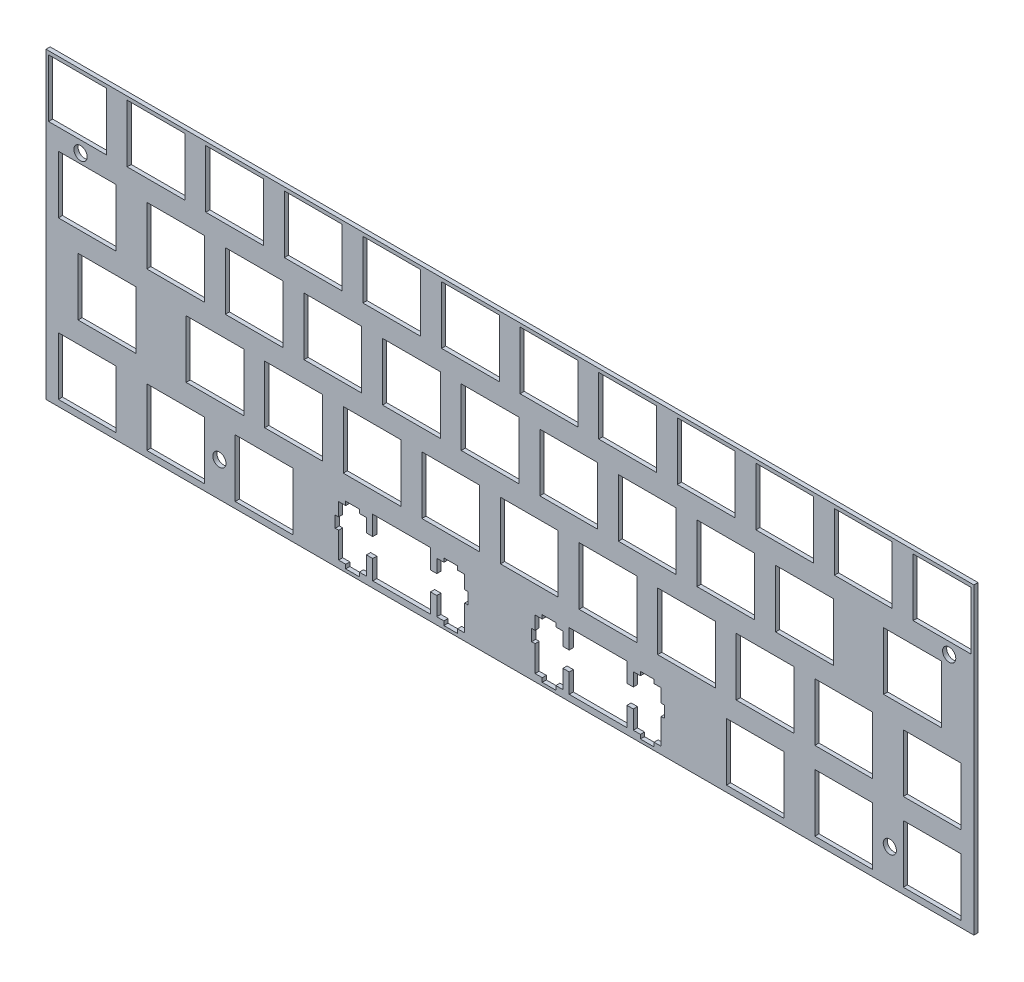
SolidWorks part; units mm, degrees
ref_plane "前视基准面" through (0, 0, 0) normal (0, 0, 1) x (1, 0, 0)
ref_plane "上视基准面" through (0, 0, 0) normal (0, 1, 0) x (1, 0, 0)
ref_plane "右视基准面" through (0, 0, 0) normal (1, 0, 0) x (0, 0, -1)
sketch "Model" plane through (0, 0, 0) normal (0, 0, 1) x (1, 0, 0)
  line L0 (227.4046, 0.7758) -> (227.4046, 75.2929) construction
  line L1 (2.0031, 74.7929) -> (226.9046, 74.7929)
  line L2 (2.0031, 74.7929) -> (2.0031, 1.2758)
  line L3 (2.0031, 1.2758) -> (226.9046, 1.2758)
  line L4 (81.201, 16.7831) -> (81.201, 12.0826)
  line L5 (81.201, 12.0826) -> (79.6756, 12.0826)
  line L6 (79.6756, 12.0826) -> (79.6756, 15.3128)
  line L7 (79.6756, 15.3128) -> (77.9501, 15.3128)
  line L8 (77.9501, 15.3128) -> (77.9501, 16.2347)
  line L9 (77.9501, 16.2347) -> (74.651, 16.2347)
  line L10 (74.651, 16.2347) -> (74.651, 15.3128)
  line L11 (74.651, 15.3128) -> (72.9259, 15.3128)
  line L12 (72.9259, 15.3128) -> (72.9259, 12.0826)
  line L13 (72.9259, 12.0826) -> (72.1004, 12.0826)
  line L14 (72.1004, 12.0826) -> (72.1004, 9.2838)
  line L15 (72.1004, 9.2838) -> (72.9259, 9.2838)
  line L16 (72.9259, 9.2838) -> (72.9259, 3.0138)
  line L17 (72.9259, 3.0138) -> (74.651, 3.0138)
  line L18 (74.651, 3.0138) -> (74.651, 2.0326)
  line L19 (74.651, 2.0326) -> (77.9501, 2.0326)
  line L20 (77.9501, 2.0326) -> (77.9501, 3.0138)
  line L21 (77.9501, 3.0138) -> (79.6756, 3.0138)
  line L22 (79.6756, 3.0138) -> (79.6756, 7.4827)
  line L23 (79.6756, 7.4827) -> (81.201, 7.4827)
  line L24 (81.201, 7.4827) -> (81.201, 2.7836)
  line L25 (81.201, 2.7836) -> (95.2003, 2.7836)
  line L26 (95.2003, 2.7836) -> (95.2003, 7.4827)
  line L27 (95.2003, 7.4827) -> (96.726, 7.4827)
  line L28 (96.726, 7.4827) -> (96.726, 3.0138)
  line L29 (96.726, 3.0138) -> (98.4497, 3.0138)
  line L30 (98.4497, 3.0138) -> (98.4497, 2.0326)
  line L31 (98.4497, 2.0326) -> (101.75, 2.0326)
  line L32 (101.75, 2.0326) -> (101.75, 3.0138)
  line L33 (101.75, 3.0138) -> (103.475, 3.0138)
  line L34 (103.475, 3.0138) -> (103.475, 9.2838)
  line L35 (103.475, 9.2838) -> (104.301, 9.2838)
  line L36 (104.301, 9.2838) -> (104.301, 12.0826)
  line L37 (104.301, 12.0826) -> (103.475, 12.0826)
  line L38 (103.475, 12.0826) -> (103.475, 15.3128)
  line L39 (103.475, 15.3128) -> (101.75, 15.3128)
  line L40 (101.75, 15.3128) -> (101.75, 16.2347)
  line L41 (101.75, 16.2347) -> (98.4497, 16.2347)
  line L42 (98.4497, 16.2347) -> (98.4497, 15.3128)
  line L43 (98.4497, 15.3128) -> (96.726, 15.3128)
  line L44 (96.726, 15.3128) -> (96.726, 12.0826)
  line L45 (96.726, 12.0826) -> (95.2003, 12.0826)
  line L46 (95.2003, 12.0826) -> (95.2003, 16.7831)
  line L47 (95.2003, 16.7831) -> (81.201, 16.7831)
  line L48 (128.826, 16.7831) -> (128.826, 12.0826)
  line L49 (128.826, 12.0826) -> (127.301, 12.0826)
  line L50 (127.301, 12.0826) -> (127.301, 15.3128)
  line L51 (127.301, 15.3128) -> (125.575, 15.3128)
  line L52 (125.575, 15.3128) -> (125.575, 16.2347)
  line L53 (125.575, 16.2347) -> (122.276, 16.2347)
  line L54 (122.276, 16.2347) -> (122.276, 15.3128)
  line L55 (122.276, 15.3128) -> (120.551, 15.3128)
  line L56 (120.551, 15.3128) -> (120.551, 12.0826)
  line L57 (120.551, 12.0826) -> (119.725, 12.0826)
  line L58 (119.725, 12.0826) -> (119.725, 9.2838)
  line L59 (119.725, 9.2838) -> (120.551, 9.2838)
  line L60 (120.551, 9.2838) -> (120.551, 3.0138)
  line L61 (120.551, 3.0138) -> (122.276, 3.0138)
  line L62 (122.276, 3.0138) -> (122.276, 2.0326)
  line L63 (122.276, 2.0326) -> (125.575, 2.0326)
  line L64 (125.575, 2.0326) -> (125.575, 3.0138)
  line L65 (125.575, 3.0138) -> (127.301, 3.0138)
  line L66 (127.301, 3.0138) -> (127.301, 7.4827)
  line L67 (127.301, 7.4827) -> (128.826, 7.4827)
  line L68 (128.826, 7.4827) -> (128.826, 2.7836)
  line L69 (128.826, 2.7836) -> (142.825, 2.7836)
  line L70 (142.825, 2.7836) -> (142.825, 7.4827)
  line L71 (142.825, 7.4827) -> (144.351, 7.4827)
  line L72 (144.351, 7.4827) -> (144.351, 3.0138)
  line L73 (144.351, 3.0138) -> (146.076, 3.0138)
  line L74 (146.076, 3.0138) -> (146.076, 2.0326)
  line L75 (146.076, 2.0326) -> (149.375, 2.0326)
  line L76 (149.375, 2.0326) -> (149.375, 3.0138)
  line L77 (149.375, 3.0138) -> (151.1, 3.0138)
  line L78 (151.1, 3.0138) -> (151.1, 9.2838)
  line L79 (151.1, 9.2838) -> (151.926, 9.2838)
  line L80 (151.926, 9.2838) -> (151.926, 12.0826)
  line L81 (151.926, 12.0826) -> (151.1, 12.0826)
  line L82 (151.1, 12.0826) -> (151.1, 15.3128)
  line L83 (151.1, 15.3128) -> (149.375, 15.3128)
  line L84 (149.375, 15.3128) -> (149.375, 16.2347)
  line L85 (149.375, 16.2347) -> (146.076, 16.2347)
  line L86 (146.076, 16.2347) -> (146.076, 15.3128)
  line L87 (146.076, 15.3128) -> (144.351, 15.3128)
  line L88 (144.351, 15.3128) -> (144.351, 12.0826)
  line L89 (144.351, 12.0826) -> (142.825, 12.0826)
  line L90 (142.825, 12.0826) -> (142.825, 16.7831)
  line L91 (142.825, 16.7831) -> (128.826, 16.7831)
  line L92 (5.0009, 16.7831) -> (19.0004, 16.7831)
  line L93 (19.0004, 16.7831) -> (19.0004, 2.7836)
  line L94 (19.0004, 2.7836) -> (5.0009, 2.7836)
  line L95 (5.0009, 2.7836) -> (5.0009, 16.7831)
  line L96 (26.4322, 16.7831) -> (40.4315, 16.7831)
  line L97 (40.4315, 16.7831) -> (40.4315, 2.7836)
  line L98 (40.4315, 2.7836) -> (26.4322, 2.7836)
  line L99 (26.4322, 2.7836) -> (26.4322, 16.7831)
  line L100 (47.8621, 16.7831) -> (61.8628, 16.7831)
  line L101 (61.8628, 16.7831) -> (61.8628, 2.7836)
  line L102 (61.8628, 2.7836) -> (47.8621, 2.7836)
  line L103 (47.8621, 2.7836) -> (47.8621, 16.7831)
  line L104 (166.926, 16.7831) -> (180.925, 16.7831)
  line L105 (180.925, 16.7831) -> (180.925, 2.7836)
  line L106 (180.925, 2.7836) -> (166.926, 2.7836)
  line L107 (166.926, 2.7836) -> (166.926, 16.7831)
  line L108 (188.357, 16.7831) -> (202.357, 16.7831)
  line L109 (202.357, 16.7831) -> (202.357, 2.7836)
  line L110 (202.357, 2.7836) -> (188.357, 2.7836)
  line L111 (188.357, 2.7836) -> (188.357, 16.7831)
  line L112 (209.787, 16.7831) -> (223.788, 16.7831)
  line L113 (223.788, 16.7831) -> (223.788, 2.7836)
  line L114 (223.788, 2.7836) -> (209.787, 2.7836)
  line L115 (209.787, 2.7836) -> (209.787, 16.7831)
  line L116 (9.762, 35.833) -> (23.7629, 35.833)
  line L117 (23.7629, 35.833) -> (23.7629, 21.8336)
  line L118 (23.7629, 21.8336) -> (9.762, 21.8336)
  line L119 (9.762, 21.8336) -> (9.762, 35.833)
  line L120 (35.9572, 35.833) -> (49.9565, 35.833)
  line L121 (49.9565, 35.833) -> (49.9565, 21.8336)
  line L122 (49.9565, 21.8336) -> (35.9572, 21.8336)
  line L123 (35.9572, 21.8336) -> (35.9572, 35.833)
  line L124 (55.0072, 35.833) -> (69.0065, 35.833)
  line L125 (69.0065, 35.833) -> (69.0065, 21.8336)
  line L126 (69.0065, 21.8336) -> (55.0072, 21.8336)
  line L127 (55.0072, 21.8336) -> (55.0072, 35.833)
  line L128 (74.0572, 35.833) -> (88.0565, 35.833)
  line L129 (88.0565, 35.833) -> (88.0565, 21.8336)
  line L130 (88.0565, 21.8336) -> (74.0572, 21.8336)
  line L131 (74.0572, 21.8336) -> (74.0572, 35.833)
  line L132 (93.1072, 35.833) -> (107.107, 35.833)
  line L133 (107.107, 35.833) -> (107.107, 21.8336)
  line L134 (107.107, 21.8336) -> (93.1072, 21.8336)
  line L135 (93.1072, 21.8336) -> (93.1072, 35.833)
  line L136 (112.157, 35.833) -> (126.157, 35.833)
  line L137 (126.157, 35.833) -> (126.157, 21.8336)
  line L138 (126.157, 21.8336) -> (112.157, 21.8336)
  line L139 (112.157, 21.8336) -> (112.157, 35.833)
  line L140 (131.207, 35.833) -> (145.207, 35.833)
  line L141 (145.207, 35.833) -> (145.207, 21.8336)
  line L142 (145.207, 21.8336) -> (131.207, 21.8336)
  line L143 (131.207, 21.8336) -> (131.207, 35.833)
  line L144 (150.257, 35.833) -> (164.257, 35.833)
  line L145 (164.257, 35.833) -> (164.257, 21.8336)
  line L146 (164.257, 21.8336) -> (150.257, 21.8336)
  line L147 (150.257, 21.8336) -> (150.257, 35.833)
  line L148 (169.307, 35.833) -> (183.307, 35.833)
  line L149 (183.307, 35.833) -> (183.307, 21.8336)
  line L150 (183.307, 21.8336) -> (169.307, 21.8336)
  line L151 (169.307, 21.8336) -> (169.307, 35.833)
  line L152 (188.357, 35.833) -> (202.357, 35.833)
  line L153 (202.357, 35.833) -> (202.357, 21.8336)
  line L154 (202.357, 21.8336) -> (188.357, 21.8336)
  line L155 (188.357, 21.8336) -> (188.357, 35.833)
  line L156 (209.787, 35.833) -> (223.788, 35.833)
  line L157 (223.788, 35.833) -> (223.788, 21.8336)
  line L158 (223.788, 21.8336) -> (209.787, 21.8336)
  line L159 (209.787, 21.8336) -> (209.787, 35.833)
  line L160 (5.0009, 54.8831) -> (19.0004, 54.8831)
  line L161 (19.0004, 54.8831) -> (19.0004, 40.8838)
  line L162 (19.0004, 40.8838) -> (5.0009, 40.8838)
  line L163 (5.0009, 40.8838) -> (5.0009, 54.8831)
  line L164 (26.4322, 54.8831) -> (40.4315, 54.8831)
  line L165 (40.4315, 54.8831) -> (40.4315, 40.8838)
  line L166 (40.4315, 40.8838) -> (26.4322, 40.8838)
  line L167 (26.4322, 40.8838) -> (26.4322, 54.8831)
  line L168 (45.4822, 54.8831) -> (59.4815, 54.8831)
  line L169 (59.4815, 54.8831) -> (59.4815, 40.8838)
  line L170 (59.4815, 40.8838) -> (45.4822, 40.8838)
  line L171 (45.4822, 40.8838) -> (45.4822, 54.8831)
  line L172 (64.5322, 54.8831) -> (78.5315, 54.8831)
  line L173 (78.5315, 54.8831) -> (78.5315, 40.8838)
  line L174 (78.5315, 40.8838) -> (64.5322, 40.8838)
  line L175 (64.5322, 40.8838) -> (64.5322, 54.8831)
  line L176 (83.5822, 54.8831) -> (97.5815, 54.8831)
  line L177 (97.5815, 54.8831) -> (97.5815, 40.8838)
  line L178 (97.5815, 40.8838) -> (83.5822, 40.8838)
  line L179 (83.5822, 40.8838) -> (83.5822, 54.8831)
  line L180 (102.632, 54.8831) -> (116.632, 54.8831)
  line L181 (116.632, 54.8831) -> (116.632, 40.8838)
  line L182 (116.632, 40.8838) -> (102.632, 40.8838)
  line L183 (102.632, 40.8838) -> (102.632, 54.8831)
  line L184 (121.682, 54.8831) -> (135.682, 54.8831)
  line L185 (135.682, 54.8831) -> (135.682, 40.8838)
  line L186 (135.682, 40.8838) -> (121.682, 40.8838)
  line L187 (121.682, 40.8838) -> (121.682, 54.8831)
  line L188 (140.732, 54.8831) -> (154.732, 54.8831)
  line L189 (154.732, 54.8831) -> (154.732, 40.8838)
  line L190 (154.732, 40.8838) -> (140.732, 40.8838)
  line L191 (140.732, 40.8838) -> (140.732, 54.8831)
  line L192 (159.782, 54.8831) -> (173.782, 54.8831)
  line L193 (173.782, 54.8831) -> (173.782, 40.8838)
  line L194 (173.782, 40.8838) -> (159.782, 40.8838)
  line L195 (159.782, 40.8838) -> (159.782, 54.8831)
  line L196 (178.832, 54.8831) -> (192.832, 54.8831)
  line L197 (192.832, 54.8831) -> (192.832, 40.8838)
  line L198 (192.832, 40.8838) -> (178.832, 40.8838)
  line L199 (178.832, 40.8838) -> (178.832, 54.8831)
  line L200 (205.026, 54.8831) -> (219.025, 54.8831)
  line L201 (219.025, 54.8831) -> (219.025, 40.8838)
  line L202 (219.025, 40.8838) -> (205.026, 40.8838)
  line L203 (205.026, 40.8838) -> (205.026, 54.8831)
  line L204 (2.6197, 73.9331) -> (16.6192, 73.9331)
  line L205 (16.6192, 73.9331) -> (16.6192, 59.9338)
  line L206 (16.6192, 59.9338) -> (2.6197, 59.9338)
  line L207 (2.6197, 59.9338) -> (2.6197, 73.9331)
  line L208 (21.6697, 73.9331) -> (35.669, 73.9331)
  line L209 (35.669, 73.9331) -> (35.669, 59.9338)
  line L210 (35.669, 59.9338) -> (21.6697, 59.9338)
  line L211 (21.6697, 59.9338) -> (21.6697, 73.9331)
  line L212 (40.7197, 73.9331) -> (54.719, 73.9331)
  line L213 (54.719, 73.9331) -> (54.719, 59.9338)
  line L214 (54.719, 59.9338) -> (40.7197, 59.9338)
  line L215 (40.7197, 59.9338) -> (40.7197, 73.9331)
  line L216 (59.7697, 73.9331) -> (73.769, 73.9331)
  line L217 (73.769, 73.9331) -> (73.769, 59.9338)
  line L218 (73.769, 59.9338) -> (59.7697, 59.9338)
  line L219 (59.7697, 59.9338) -> (59.7697, 73.9331)
  line L220 (78.8197, 73.9331) -> (92.819, 73.9331)
  line L221 (92.819, 73.9331) -> (92.819, 59.9338)
  line L222 (92.819, 59.9338) -> (78.8197, 59.9338)
  line L223 (78.8197, 59.9338) -> (78.8197, 73.9331)
  line L224 (97.8683, 73.9331) -> (111.869, 73.9331)
  line L225 (111.869, 73.9331) -> (111.869, 59.9338)
  line L226 (111.869, 59.9338) -> (97.8683, 59.9338)
  line L227 (97.8683, 59.9338) -> (97.8683, 73.9331)
  line L228 (116.918, 73.9331) -> (130.919, 73.9331)
  line L229 (130.919, 73.9331) -> (130.919, 59.9338)
  line L230 (130.919, 59.9338) -> (116.918, 59.9338)
  line L231 (116.918, 59.9338) -> (116.918, 73.9331)
  line L232 (135.97, 73.9331) -> (149.969, 73.9331)
  line L233 (149.969, 73.9331) -> (149.969, 59.9338)
  line L234 (149.969, 59.9338) -> (135.97, 59.9338)
  line L235 (135.97, 59.9338) -> (135.97, 73.9331)
  line L236 (155.02, 73.9331) -> (169.019, 73.9331)
  line L237 (169.019, 73.9331) -> (169.019, 59.9338)
  line L238 (169.019, 59.9338) -> (155.02, 59.9338)
  line L239 (155.02, 59.9338) -> (155.02, 73.9331)
  line L240 (174.07, 73.9331) -> (188.069, 73.9331)
  line L241 (188.069, 73.9331) -> (188.069, 59.9338)
  line L242 (188.069, 59.9338) -> (174.07, 59.9338)
  line L243 (174.07, 59.9338) -> (174.07, 73.9331)
  line L244 (193.12, 73.9331) -> (207.119, 73.9331)
  line L245 (207.119, 73.9331) -> (207.119, 59.9338)
  line L246 (207.119, 59.9338) -> (193.12, 59.9338)
  line L247 (193.12, 59.9338) -> (193.12, 73.9331)
  line L248 (212.17, 73.9331) -> (226.169, 73.9331)
  line L249 (226.169, 73.9331) -> (226.169, 59.9338)
  line L250 (226.169, 59.9338) -> (212.17, 59.9338)
  line L251 (212.17, 59.9338) -> (212.17, 73.9331)
  line L254 (226.9046, 74.7929) -> (226.9046, 1.2758)
  line L255 (1.5031, 0.7758) -> (69.2125, 0.7758) construction
  line L256 (227.4046, 75.2929) -> (1.5031, 75.2929) construction
  line L257 (1.5031, 75.2929) -> (1.5031, 0.7758) construction
  circle A0 centre (10.3762, 57.1659) radius 1.6
  circle A1 centre (44.0312, 9.6488) radius 1.6
  circle A2 centre (206.5316, 9.6488) radius 1.6
  circle A3 centre (220.9176, 57.1659) radius 1.6
  dimension "D1" = 0.5
  dimension "D2" = 0.5
  dimension "D3" = 0.5
  dimension "D4" = 0.5
extrude "凸台-拉伸1" add sketch "Model" along normal blind 1
